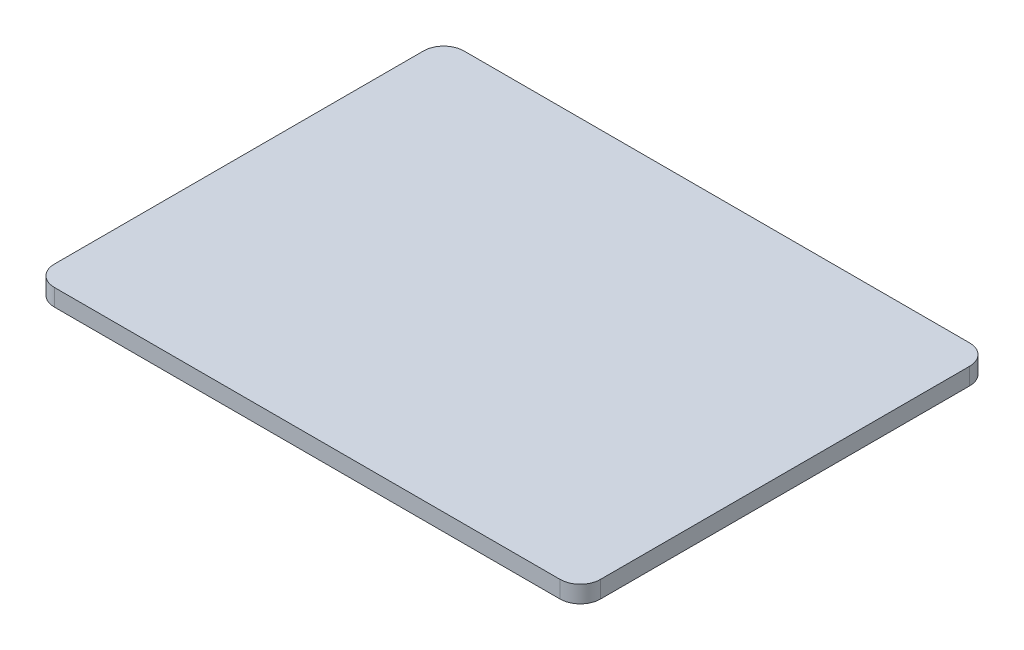
SolidWorks part; units mm, degrees
ref_plane "Front Plane" through (0, 0, 0) normal (0, 0, 1) x (1, 0, 0)
ref_plane "Top Plane" through (0, 0, 0) normal (0, 1, 0) x (1, 0, 0)
ref_plane "Right Plane" through (0, 0, 0) normal (1, 0, 0) x (0, 0, -1)
sketch "Sketch1" plane through (0, 0, 0) normal (0, 1, 0) x (1, 0, 0)
  line L0 (0, 0) -> (0, 658.1501) construction
  line L1 (0, 0) -> (593.1885, 0) construction
  line L3 (-376.4, 304.8) -> (376.4, 304.8)
  line L4 (-406.4, 274.8) -> (-406.4, -274.8)
  line L5 (-376.4, -304.8) -> (376.4, -304.8)
  line L6 (406.4, 274.8) -> (406.4, -274.8)
  arc A0 (376.4, -304.8) -> (406.4, -274.8) centre (376.4, -274.8) ccw
  arc A1 (-376.4, -304.8) -> (-406.4, -274.8) centre (-376.4, -274.8) cw
  arc A2 (406.4, 274.8) -> (376.4, 304.8) centre (376.4, 274.8) ccw
  arc A3 (-376.4, 304.8) -> (-406.4, 274.8) centre (-376.4, 274.8) ccw
  point P11 (406.4, -304.8)
  point P16 (406.4, 304.8)
  point P19 (-406.4, 304.8)
  dimension "D3" = 30
  dimension "D1" = 812.8
  dimension "D2" = 609.6
extrude "Boss-Extrude1" add sketch "Sketch1" along normal blind 25.4
